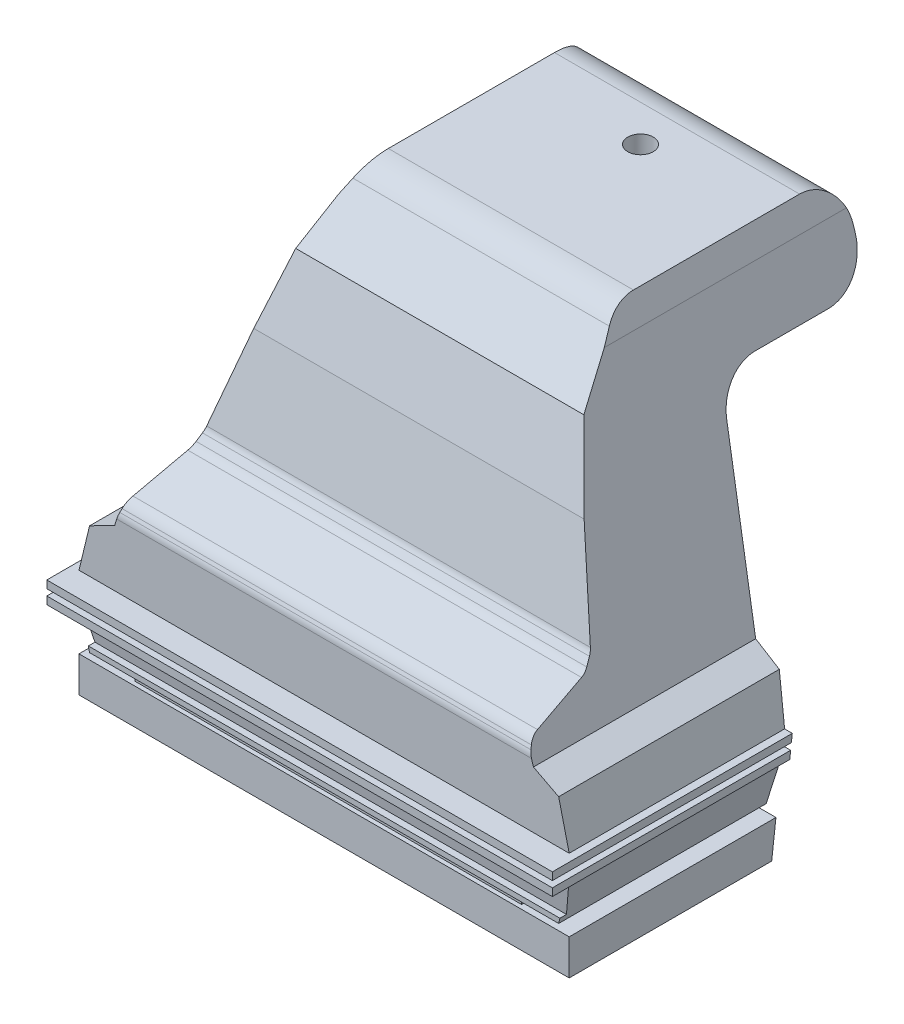
SolidWorks part; units mm, degrees
ref_plane "Front Plane" through (0, 0, 0) normal (0, 0, 1) x (1, 0, 0)
ref_plane "Top Plane" through (0, 0, 0) normal (0, 1, 0) x (1, 0, 0)
ref_plane "Right Plane" through (0, 0, 0) normal (1, 0, 0) x (0, 0, -1)
sketch "Sketch4" plane through (0, 0, 0) normal (0, 0, 1) x (1, 0, 0)
  line L0 (0, 0) -> (0, 90) construction
  line L1 (0, 90) -> (25, 90)
  line L2 (0, 0) -> (50, 0)
  line L3 (50, 0) -> (50, 7.272)
  line L4 (50, 7.272) -> (39.4414, 7.272)
  line L5 (39.4414, 7.272) -> (39.4414, 8.5567)
  line L6 (39.4414, 8.5567) -> (47.8501, 8.5567)
  line L7 (47.8501, 8.5567) -> (50, 17.6661)
  line L8 (50, 17.6661) -> (51.5683, 17.6661)
  line L9 (51.5683, 17.6661) -> (51.5683, 19.2118)
  line L10 (51.5683, 19.2118) -> (50, 19.2118)
  line L11 (50, 19.2118) -> (50, 20.4866)
  line L12 (50, 20.4866) -> (51.5683, 20.4866)
  line L13 (51.5683, 20.4866) -> (51.5683, 22.0385)
  line L14 (51.5683, 22.0385) -> (50, 22.0385)
  line L15 (50, 22.0385) -> (47.8501, 30.9563)
  line L16 (47.8501, 30.9563) -> (42.7056, 33.6258)
  line L17 (42.7056, 33.6258) -> (27.11, 84.9048)
  line L18 (27.11, 84.9048) -> (25, 90)
  line L19 (0, 90) -> (0, 0)
  dimension "D1" = 90
extrude "Boss-Extrude2" add sketch "Sketch4" along normal blind 80
sketch "Sketch5" plane through (0, 0, 0) normal (-1, 0, 0) x (0, 0, 1)
  line L0 (0, 72.6495) -> (30, 72.6495)
  line L1 (0, 90) -> (0, 0) construction
  line L2 (30, 72.6495) -> (38.6904, 0)
  line L3 (80, 0) -> (0, 0) construction
  line L4 (38.6904, 0) -> (0, 0)
  line L5 (0, 0) -> (0, 72.6495)
  line L6 (45.5691, 90) -> (57.7079, 75.8866)
  line L7 (80, 90) -> (0, 90) construction
  line L8 (57.7079, 75.8866) -> (65.4102, 42.8019)
  line L9 (65.4102, 42.8019) -> (80, 37.5744)
  line L10 (80, 90) -> (80, 0) construction
  line L11 (80, 37.5744) -> (80, 90)
  line L12 (80, 90) -> (45.5691, 90)
  line L13 (45.5691, 90) -> (45.0296, 90.3183)
  point P13 (66.1973, 33.1735)
  point P21 (80, 37.5744)
  point P22 (65.4102, 42.8019)
  line M1 (0, 90) -> (0, 0)
  line M2 (0, 0) -> (80, 0)
  line M3 (80, 0) -> (80, 90)
  line M4 (80, 90) -> (0, 90)
extrude "Cut-Extrude6" cut sketch "Sketch5" against normal blind 80 contours L8 L9 L6 M3 M4 | L2 L0 M1 M2
fillet "Fillet4" radius 8 2 edges at (15.4186, 72.6495, 0) (15.4186, 72.6495, 30)
fillet "Fillet6" radius 8 2 edges at (12.5, 90, 0) (12.5, 90, 45.5691)
sketch "Sketch6" plane through (0, 0, 80) normal (0, 0, 1) x (1, 0, 0)
  line L0 (50, 22.0385) -> (0, 22.0385)
  line L1 (50, 20.4866) -> (0, 20.4866)
  line L2 (50, 19.2118) -> (0, 19.2118)
  line L3 (50, 17.6661) -> (0, 17.6661)
  line L4 (0, 22.0385) -> (0, 17.6661)
  line L17 (47.8501, 30.9563) -> (42.7056, 33.6258)
  line L18 (41.5047, 37.5744) -> (0, 37.5744)
  line L19 (0, 37.5744) -> (0, 0)
  line L20 (0, 0) -> (50, 0)
  line L21 (50, 0) -> (50, 7.272)
  line L22 (50, 7.272) -> (39.4414, 7.272)
  line L23 (39.4414, 7.272) -> (39.4414, 8.5567)
  line L24 (39.4414, 8.5567) -> (47.8501, 8.5567)
  line L25 (47.8501, 8.5567) -> (50, 17.6661)
  line L26 (50, 17.6661) -> (51.5683, 17.6661)
  line L27 (51.5683, 17.6661) -> (51.5683, 19.2118)
  line L28 (51.5683, 19.2118) -> (50, 19.2118)
  line L29 (50, 19.2118) -> (50, 20.4866)
  line L30 (50, 20.4866) -> (51.5683, 20.4866)
  line L31 (51.5683, 20.4866) -> (51.5683, 22.0385)
  line L32 (51.5683, 22.0385) -> (50, 22.0385)
  line L33 (50, 22.0385) -> (47.8501, 30.9563)
  line L36 (0, 22.0385) -> (0, 17.6661)
  line L41 (41.5047, 37.5744) -> (0, 37.5744)
  line L42 (42.7056, 33.6258) -> (41.5047, 37.5744)
  line L43 (50, 17.6661) -> (51.5683, 17.6661)
  line L44 (51.5683, 17.6661) -> (51.5683, 19.2118)
  line L45 (51.5683, 19.2118) -> (50, 19.2118)
  line L46 (42.7056, 33.6258) -> (41.5047, 37.5744)
  line L47 (50, 20.4866) -> (51.5683, 20.4866)
  line L48 (51.5683, 20.4866) -> (51.5683, 22.0385)
  line L49 (51.5683, 22.0385) -> (50, 22.0385)
  line M20 (0, 37.5744) -> (0, 0)
  line M27 (50, 17.6661) -> (51.5683, 17.6661)
  line M28 (51.5683, 17.6661) -> (51.5683, 19.2118)
  line M29 (51.5683, 19.2118) -> (50, 19.2118)
  line M31 (50, 20.4866) -> (51.5683, 20.4866)
  line M32 (51.5683, 20.4866) -> (51.5683, 22.0385)
  line M33 (51.5683, 22.0385) -> (50, 22.0385)
  dimension "D1" = 0
extrude "Boss-Extrude3" add sketch "Sketch6" along normal blind 5 contours L1 L0 M31 M32 M33 M20 | L3 L2 M27 M28 M29 M20
sketch "Sketch7" plane through (0, 0, 0) normal (-1, 0, 0) x (0, 0, 1)
  line L0 (80, 17.6661) -> (78.658, 9.6134)
  line L1 (78.658, 9.6134) -> (80, 9.6134)
  line L2 (80, 17.6661) -> (80, 0) construction
  line L3 (80, 9.6134) -> (80, 17.6661)
extrude "Cut-Extrude7" cut sketch "Sketch7" against normal blind 53
sketch "Sketch8" plane through (39.4414, 0, 0) normal (1, 0, 0) x (0, 0, -1)
  line L0 (-80, 8.5567) -> (-37.6668, 8.5567) construction
  line L1 (-80, 7.272) -> (-79.1379, 7.272)
  line L2 (-80, 7.272) -> (-80, 8.5567)
  line L3 (-80, 8.5567) -> (-79.1379, 8.5567)
  line L4 (-79.1379, 7.272) -> (-79.1379, 8.5567)
extrude "Cut-Extrude8" cut sketch "Sketch8" against normal blind 53
sketch "Sketch9" plane through (0, 72.6495, 0) normal (0, -1, 0) x (1, 0, 0)
  line L0 (0, 8) -> (0, 22.8999) construction
  circle A0 centre (0, 15.45) radius 2.6
extrude "Cut-Extrude9" cut sketch "Sketch9" against normal blind 53
chamfer "Chamfer1" distance 2 angle 10 1 edges at (2.6, 72.6495, 15.45)
chamfer "Chamfer2" distance 2 angle 24 3 edges at (14.9264, 75.8866, 57.7079) (19.9574, 42.8019, 65.4102) (20.7523, 37.5744, 80)
fillet "Fillet7" radius 3 4 edges at (21.0565, 35.5744, 80) (20.6946, 37.954, 78.9405) (20.0337, 42.3005, 66.8094) (19.6612, 44.7498, 64.9567)
mirror "Mirror2" about plane through (0, 90, 80) normal (1, 0, 0) of bodies 113
